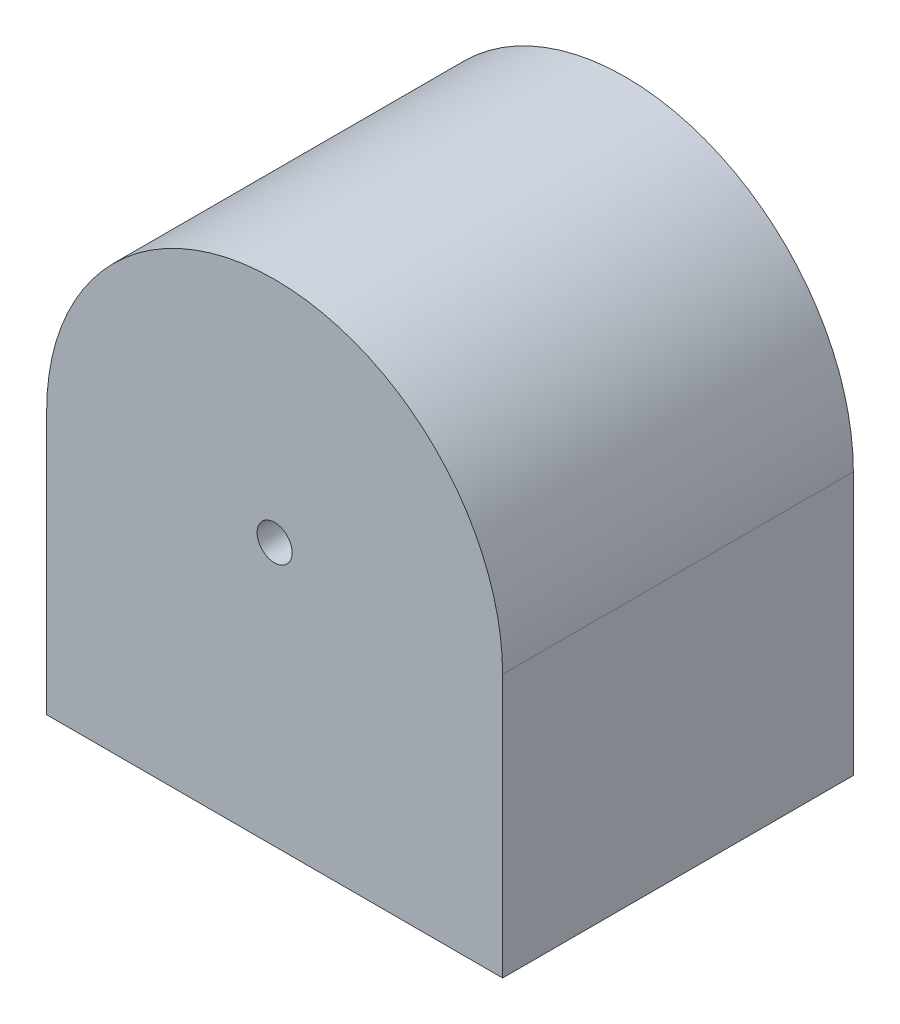
SolidWorks part; units mm, degrees
ref_plane "Alzado" through (0, 0, 0) normal (0, 0, 1) x (1, 0, 0)
ref_plane "Planta" through (0, 0, 0) normal (0, 1, 0) x (1, 0, 0)
ref_plane "Vista lateral" through (0, 0, 0) normal (1, 0, 0) x (0, 0, -1)
sketch "Croquis1" plane through (0, 0, 0) normal (0, 0, 1) x (1, 0, 0)
  line L0 (-65, 0) -> (-65, -65)
  line L2 (65, -65) -> (65, 0)
  line L4 (0, -75) -> (-65, -75)
  line L5 (-65, -75) -> (-65, -65)
  line L6 (0, -75) -> (65, -75)
  line L7 (65, -75) -> (65, -65)
  arc A0 (65, 0) -> (-65, 0) centre (0, 0) ccw
extrude "Saliente-Extruir1" add sketch "Croquis1" along normal blind 100 contours L6 L7 L2 A0 L0 L5 L4
shell "Vaciado1" thickness 10
sketch "Croquis4" plane through (0, 0, 100) normal (0, 0, 1) x (1, 0, 0)
  circle A0 centre (0, 0) radius 5
extrude "Cortar-Extruir1" cut sketch "Croquis4" against normal blind 130
